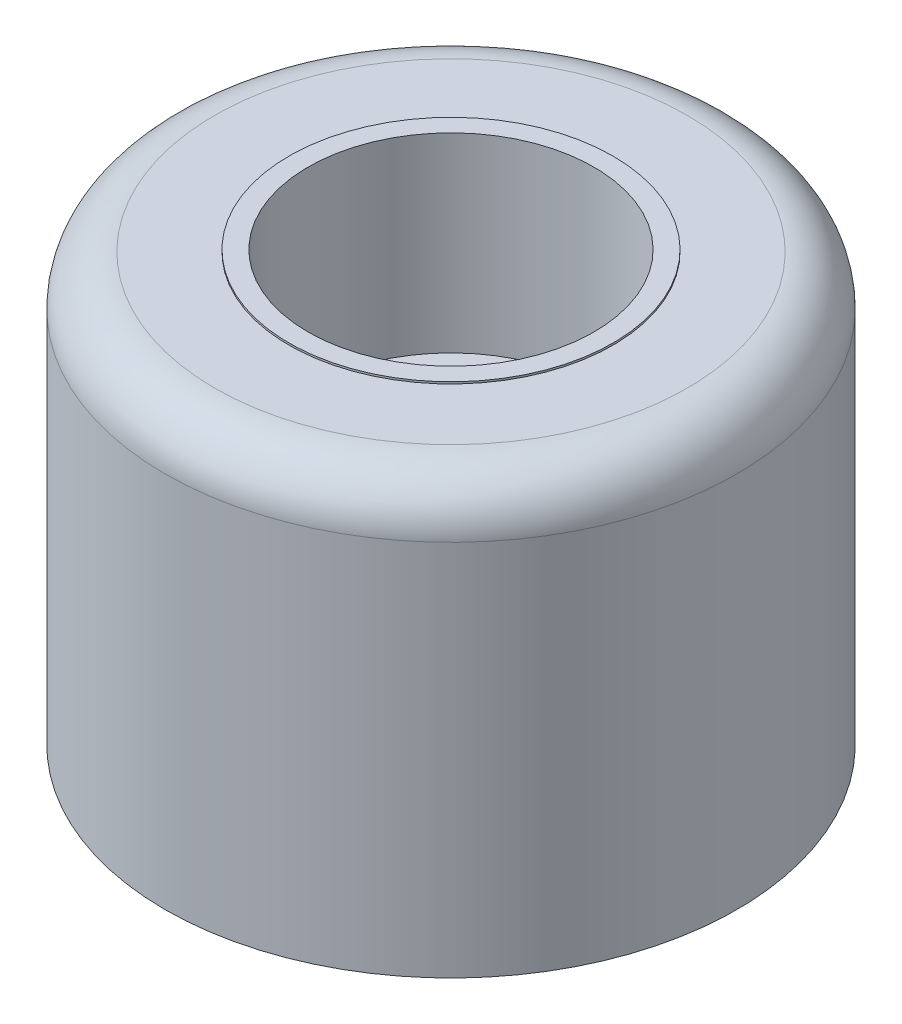
SolidWorks part; units mm, degrees
ref_plane "Front Plane" through (0, 0, 0) normal (0, 0, 1) x (1, 0, 0)
ref_plane "Top Plane" through (0, 0, 0) normal (0, 1, 0) x (1, 0, 0)
ref_plane "Right Plane" through (0, 0, 0) normal (1, 0, 0) x (0, 0, -1)
sketch "Sketch1" plane through (0, 0, 0) normal (0, 0, 1) x (1, 0, 0)
  line L0 (0, -7.9375) -> (0, 6.35) construction
sketch "Sketch2" plane through (0, 0, 0) normal (0, 1, 0) x (1, 0, 0)
  line L0 (0, -9.525) -> (0, 9.525) construction
  line L1 (2.3813, 0) -> (-2.3813, 0)
  line L2 (4.7625, 0) -> (-4.7625, 0) construction
  point P4 (0, 0)
  point P8 (0, 0)
  point P11 (0, 0)
  dimension "OD" = 19.05
  dimension "Mounting-Hole-Dia" = 4.7625
  dimension "Counterbore-Dia" = 9.525
sketch "Sketch3" plane through (0, 0, 0) normal (0, 1, 0) x (1, 0, 0)
  circle A0 centre (0, 0) radius 9.525
  circle A1 centre (0, 0) radius 2.3813
extrude "Boss-Extrude1" add sketch "Sketch3" along normal up to vertex (6.35 mm away) and the other way up to vertex (7.9375 mm away) up to point (0, 6.35, 0) other way up to point (0, -7.9375, 0)
sketch "Sketch4" plane through (0, 0, 0) normal (0, 1, 0) x (1, 0, 0)
  circle A0 centre (0, 0) radius 4.7625
extrude "Cut-Extrude1" cut sketch "Sketch4" along normal up to surface (6.35 mm away) up to face at (0, 6.35, 9.525)
sketch "Sketch5" plane through (0, 0, 0) normal (0, 0, 1) x (1, 0, 0)
  line L0 (-9.525, -7.9375) -> (9.525, -7.9375) construction
  line L5 (-9.525, 6.35) -> (-5.3975, 6.35)
  line L6 (-9.525, 6.35) -> (-9.525, 6.2865)
  line L7 (-9.525, 6.2865) -> (-5.3975, 6.2865)
  line L8 (-5.3975, 6.35) -> (-5.3975, 6.2865)
  dimension "D1" = 14.224
  dimension "D2" = 0.635
revolve "Cut-Revolve1" cut sketch "Sketch5" angle 360 about L0
fillet "Fillet2" radius 1.651 1 edges at (0, 6.2865, -9.525)
equation "\"D1@Sketch5\"=\"Height@Sketch1\" - 0.0025"
